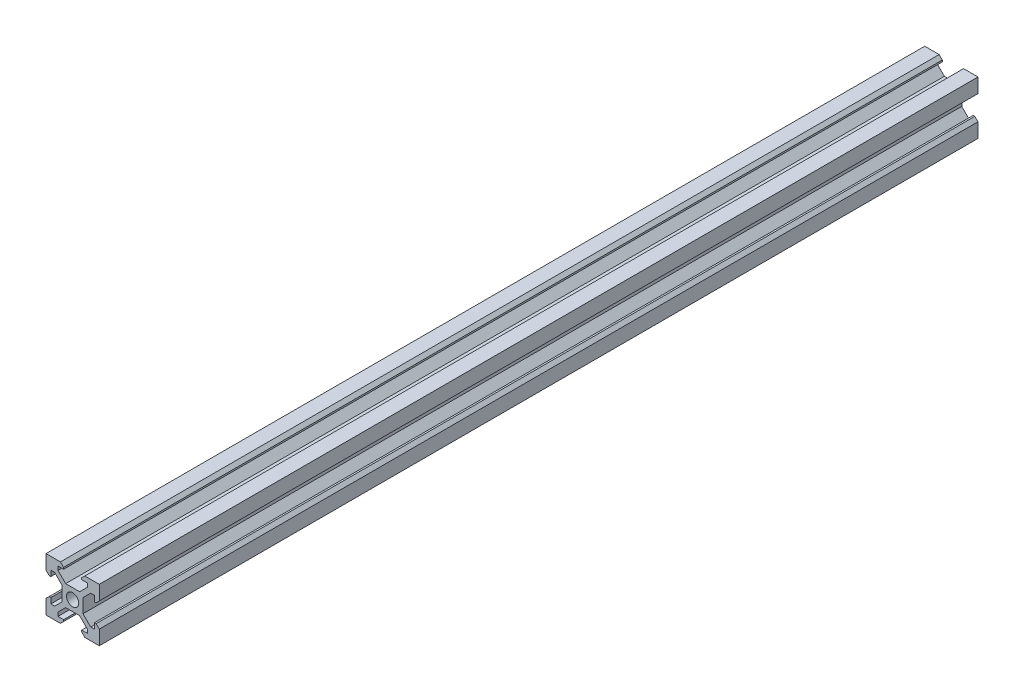
SolidWorks part; units mm, degrees
ref_plane "Front Plane" through (0, 0, 0) normal (0, 0, 1) x (1, 0, 0)
ref_plane "Top Plane" through (0, 0, 0) normal (0, 1, 0) x (1, 0, 0)
ref_plane "Right Plane" through (0, 0, 0) normal (1, 0, 0) x (0, 0, -1)
sketch "Sketch1" plane through (0, 0, 0) normal (0, 0, 1) x (1, 0, 0)
  line L1 (0, 0) -> (20, 0)
  line L2 (0, 0) -> (0, 20)
  line L3 (0, 20) -> (20, 20)
  line L4 (20, 0) -> (20, 20)
  dimension "D1" = 20
extrude "Boss-Extrude1" add sketch "Sketch1" against normal blind 330
sketch "Sketch2" plane through (0, 0, 0) normal (0, 0, 1) x (1, 0, 0)
  line L12 (0, 10) -> (20, 10) construction
  line L13 (5.42, 20) -> (14.58, 20)
  line L14 (0, 20) -> (0, 0) construction
  line L15 (20, 20) -> (0, 20) construction
  line L16 (20, 0) -> (20, 20) construction
  line L17 (20, 20) -> (0, 0) construction
  line L18 (14.58, 20) -> (13.395, 18.815)
  line L55 (13.395, 18.815) -> (13.395, 18.2)
  line L56 (13.395, 18.2) -> (15.5, 18.2)
  line L57 (15.5, 18.2) -> (15.5, 16.7728)
  line L58 (15.5, 16.7728) -> (12.6272, 13.9)
  line L59 (12.6272, 13.9) -> (7.3728, 13.9)
  line L60 (7.3728, 13.9) -> (4.5, 16.7728)
  line L61 (4.5, 16.7728) -> (4.5, 18.2)
  line L62 (4.5, 18.2) -> (6.605, 18.2)
  line L63 (6.605, 18.2) -> (6.605, 18.815)
  line L64 (6.605, 18.815) -> (5.42, 20)
  line L65 (6.605, 1.185) -> (5.42, 0)
  line L66 (6.605, 1.8) -> (6.605, 1.185)
  line L67 (4.5, 1.8) -> (6.605, 1.8)
  line L68 (4.5, 3.2272) -> (4.5, 1.8)
  line L69 (7.3728, 6.1) -> (4.5, 3.2272)
  line L70 (12.6272, 6.1) -> (7.3728, 6.1)
  line L71 (15.5, 3.2272) -> (12.6272, 6.1)
  line L72 (15.5, 1.8) -> (15.5, 3.2272)
  line L73 (13.395, 1.8) -> (15.5, 1.8)
  line L74 (13.395, 1.185) -> (13.395, 1.8)
  line L75 (14.58, 0) -> (13.395, 1.185)
  line L76 (5.42, 0) -> (14.58, 0)
  line L77 (20, 0) -> (0, 20) construction
  line L78 (1.8, 6.605) -> (1.185, 6.605)
  line L79 (1.8, 4.5) -> (1.8, 6.605)
  line L80 (3.2272, 4.5) -> (1.8, 4.5)
  line L81 (6.1, 7.3728) -> (3.2272, 4.5)
  line L82 (6.1, 12.6272) -> (6.1, 7.3728)
  line L83 (3.2272, 15.5) -> (6.1, 12.6272)
  line L84 (1.8, 15.5) -> (3.2272, 15.5)
  line L85 (1.8, 13.395) -> (1.8, 15.5)
  line L86 (1.185, 13.395) -> (1.8, 13.395)
  line L87 (0, 14.58) -> (1.185, 13.395)
  line L88 (0, 5.42) -> (0, 14.58)
  line L89 (1.185, 6.605) -> (0, 5.42)
  line L90 (18.815, 6.605) -> (20, 5.42)
  line L91 (18.2, 6.605) -> (18.815, 6.605)
  line L92 (18.2, 4.5) -> (18.2, 6.605)
  line L93 (16.7728, 4.5) -> (18.2, 4.5)
  line L94 (13.9, 7.3728) -> (16.7728, 4.5)
  line L95 (13.9, 12.6272) -> (13.9, 7.3728)
  line L96 (16.7728, 15.5) -> (13.9, 12.6272)
  line L97 (18.2, 15.5) -> (16.7728, 15.5)
  line L98 (18.2, 13.395) -> (18.2, 15.5)
  line L99 (18.815, 13.395) -> (18.2, 13.395)
  line L100 (20, 14.58) -> (18.815, 13.395)
  line L101 (20, 5.42) -> (20, 14.58)
  circle A0 centre (10, 10) radius 2.3
  point P19 (13.395, 18.5075)
  point P63 (10, 13.9)
  point P64 (10, 20)
  point P65 (10, 20)
  dimension "D8" = 4.6
  dimension "D1" = 90
  dimension "D2" = 11
  dimension "D3" = 9.16
  dimension "D4" = 6.79
  dimension "D5" = 1.8
  dimension "D6" = 4.3
  dimension "D7" = 1.8
extrude "Cut-Extrude1" cut sketch "Sketch2" against normal through all
